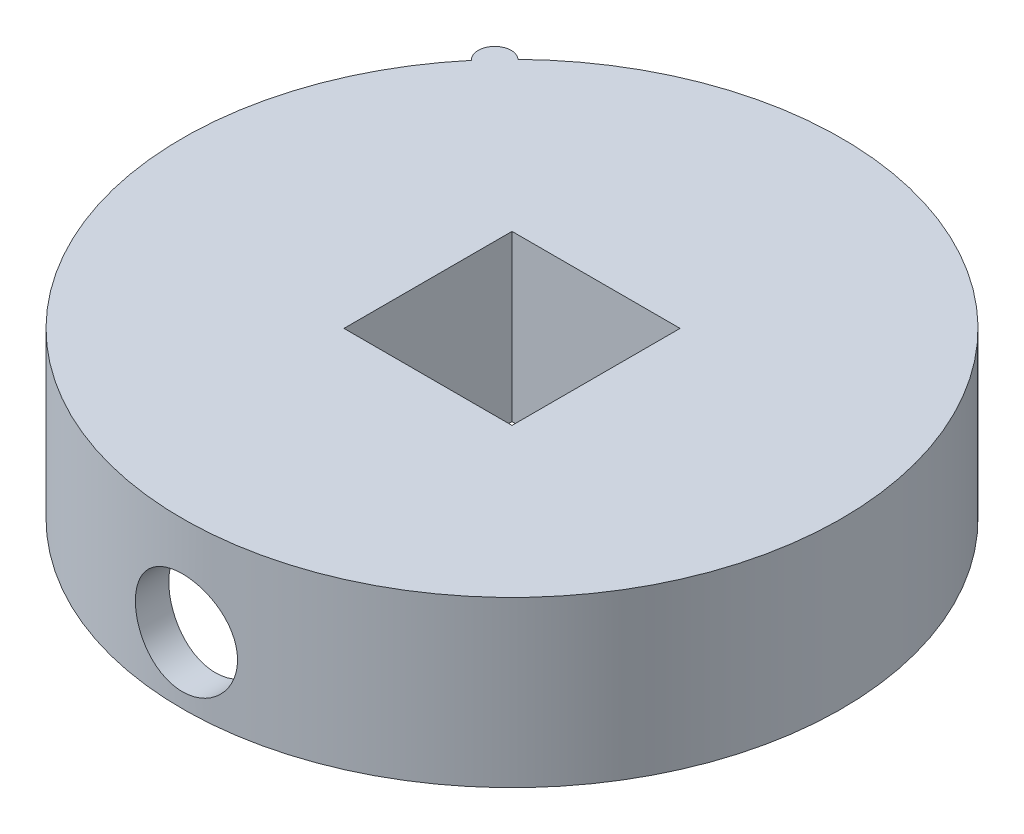
SolidWorks part; units mm, degrees
ref_plane "Спереди" through (0, 0, 0) normal (0, 0, 1) x (1, 0, 0)
ref_plane "Сверху" through (0, 0, 0) normal (0, 1, 0) x (1, 0, 0)
ref_plane "Справа" through (0, 0, 0) normal (1, 0, 0) x (0, 0, -1)
sketch "Sketch1" plane through (0, 0, 0) normal (0, 1, 0) x (1, 0, 0)
  circle A0 centre (0, 0) radius 20
  dimension "D1" = 40
extrude "Boss-Extrude1" add sketch "Sketch1" along normal blind 10
sketch "Sketch2" plane through (0, 0, 0) normal (0, -1, 0) x (1, 0, 0)
  line L1 (5.1, 5.1) -> (-5.1, 5.1)
  line L2 (5.1, 5.1) -> (5.1, -5.1)
  line L3 (5.1, -5.1) -> (-5.1, -5.1)
  line L4 (-5.1, 5.1) -> (-5.1, -5.1)
  line L5 (5.1, 5.1) -> (-5.1, -5.1) construction
  line L6 (5.1, -5.1) -> (-5.1, 5.1) construction
  point P0 (0, 0)
  dimension "D1" = 10.2
extrude "Cut-Extrude2" cut sketch "Sketch2" against normal through all
shell "Shell3" thickness 2
sketch "Sketch3" plane through (0, 0, 7.1) normal (0, 0, 1) x (1, 0, 0)
  line L0 (0, 8) -> (0, 0) construction
  line L1 (7.1, 8) -> (-7.1, 8) construction
  line L2 (7.1, 0) -> (-7.1, 0) construction
  circle A0 centre (0, 4) radius 3.1
  dimension "D1" = 6.2
extrude "Cut-Extrude3" cut sketch "Sketch3" along normal through all
sketch "Sketch4" plane through (0, 10, 0) normal (0, 1, 0) x (1, 0, 0)
  line L0 (0, 0) -> (-20, 0) construction
  line L1 (-20, 0) -> (-15.3209, 12.8558) construction
  line L2 (-15.3209, 12.8558) -> (0, 0) construction
  line L3 (-13.9603, 14.3216) -> (-15.3209, 12.8558)
  circle A0 centre (0, 0) radius 20 construction
  arc A1 (-15.3209, 12.8558) -> (-13.9603, 14.3216) centre (-14.6406, 13.5887) cw
  dimension "D2" = 1
  dimension "D1" = 40
  dimension "D3" = 2
extrude "Boss-Extrude2" add sketch "Sketch4" against normal up to surface (10 mm away) up to face at (0, 0, 18)
